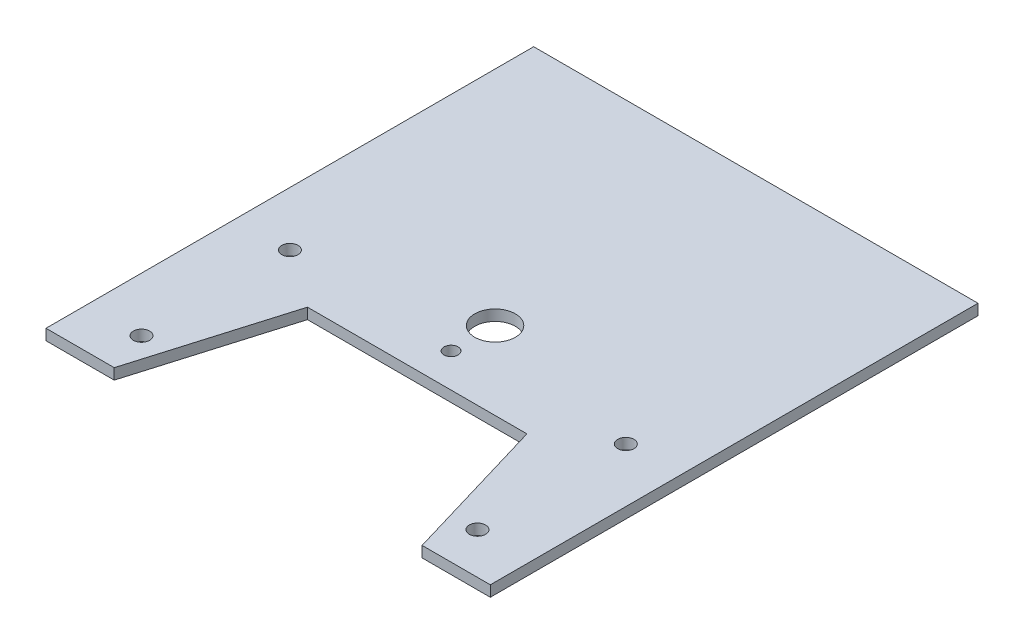
SolidWorks part; units mm, degrees
ref_plane "Front Plane" through (0, 0, 0) normal (0, 0, 1) x (1, 0, 0)
ref_plane "Top Plane" through (0, 0, 0) normal (0, 1, 0) x (1, 0, 0)
ref_plane "Right Plane" through (0, 0, 0) normal (1, 0, 0) x (0, 0, -1)
sketch "Sketch1" plane through (0, 0, 0) normal (0, 1, 0) x (1, 0, 0)
  line L0 (85, -185) -> (40.5, -35)
  line L1 (-82, 90) -> (82, 90)
  line L2 (-82, 90) -> (-82, -90)
  line L3 (-82, -90) -> (82, -90)
  line L4 (82, 90) -> (82, -90)
  line L5 (-82, 90) -> (82, -90) construction
  line L6 (-82, -90) -> (82, 90) construction
  line L7 (-40.5, -35) -> (-85, -185)
  line L8 (85, -185) -> (-85, -185)
  line L9 (40.5, -35) -> (-40.5, -35)
  line L10 (0, 90) -> (0, -90) construction
  point P0 (0, 0)
  point P8 (0, -35)
  point P13 (0, -185)
  dimension "D1" = 164
  dimension "D2" = 180
  dimension "D3" = 81
  dimension "D4" = 85
  dimension "D5" = 55
  dimension "D6" = 85
  dimension "D7" = 150
extrude "Boss-Extrude3" add sketch "Sketch1" along normal blind 4 contours L9 L0 L3 L4 L1 L2 L7
sketch "Sketch3" plane through (-73, 4, 0) normal (0, 1, 0) x (0, 0, 1)
  line L0 (-90, -9) -> (-0.5, -9)
  line L1 (-90, 73) -> (35, 73) construction
  line L2 (-90, -1) -> (-0.5, -1)
  line L12 (-90, -9) -> (-90, 155) construction
  line L18 (35, 113.5) -> (35, 32.5) construction
  line L23 (-0.5, -9) -> (-0.5, 155) construction
  line L24 (-90, -9) -> (-0.5, -9)
  line L25 (-90, -9) -> (-90, -1)
  line L26 (-90, -1) -> (-0.5, -1)
  line L27 (-0.5, -9) -> (-0.5, -1)
  line L28 (-90, 155) -> (90, 155) construction
  line L29 (-90, -5) -> (-0.5, -5) construction
  line L34 (-90, 151) -> (-0.5, 151) construction
  line L37 (-90, 147) -> (-0.5, 147)
  line L38 (-90, 147) -> (-82, 147)
  line L39 (-90, 147) -> (-90, -1)
  line L40 (-90, -1) -> (-82, -1)
  line L41 (-82, 147) -> (-82, -1)
  line L42 (-86, -1) -> (-86, 147) construction
  line L43 (-0.5, 155) -> (-0.5, 147)
  line L44 (-90, 155) -> (-0.5, 155)
  line L45 (-90, 155) -> (-90, 147)
  line L51 (35, 32.5) -> (90, 16.1833) construction
  line L52 (90, -9) -> (82, -9)
  line L53 (90, -9) -> (90, 18.5567)
  line L54 (90, 18.5567) -> (82, 18.5567)
  line L55 (82, -9) -> (82, 18.5567)
  circle A11 centre (-45.25, -5) radius 2.1
  circle A25 centre (-86, -5) radius 2.1
  circle A26 centre (-86, 34) radius 2.1
  circle A27 centre (-86, 73) radius 2.1
  circle A28 centre (-86, 112) radius 2.1
  circle A29 centre (-86, 151) radius 2.1
  circle A30 centre (-4.5, -5) radius 2.1
  circle A31 centre (-4.5, 151) radius 2.1
  circle A32 centre (-45.25, 151) radius 2.1
  circle A33 centre (86, 7.59) radius 2.1
  circle A34 centre (86, 138.41) radius 2.1
  point P38 (-82, 73)
  dimension "D1" = 8
  dimension "D2" = 89.5
  dimension "D4" = 4.2
  dimension "D3" = 8
  dimension "D5" = 40.75
  dimension "D6" = 5
  dimension "D7" = 4
  dimension "D8" = 8
  dimension "D9" = 4
  dimension "D10" = 16.59
extrude "Cut-Extrude2" [suppressed] cut sketch "Sketch3" against normal blind 10
sketch "Sketch5" plane through (0, 4, 0) normal (0, 1, 0) x (1, 0, 0)
  line L0 (82, 90) -> (82, -90) construction
  line L1 (56.8167, -90) -> (82, -90) construction
  line L2 (0, 90) -> (0, -35) construction
  line L3 (-82, 90) -> (82, 90) construction
  line L4 (40.5, -35) -> (-40.5, -35) construction
  circle A0 centre (62, -74.75) radius 3
  circle A1 centre (62, -19.99) radius 3
  circle A2 centre (-62, -74.75) radius 3
  circle A3 centre (-62, -19.99) radius 3
  circle A4 centre (0, -6.25) radius 7.5
  circle A5 centre (0, -22.5) radius 2.6
  dimension "D1" = 6
  dimension "D5" = 15
  dimension "D7" = 5.2
  dimension "D2" = 20
  dimension "D3" = 15.25
  dimension "D4" = 54.76
  dimension "D6" = 28.75
  dimension "D8" = 16.25
extrude "Cut-Extrude3" cut sketch "Sketch5" against normal up to next contours A2 | A3 | A0 | A1 | A4 | A5
sketch "Sketch6" plane through (0, 4, 0) normal (0, 1, 0) x (1, 0, 0)
  line L0 (0, 90) -> (0, -35) construction
  line L1 (-82, 90) -> (82, 90) construction
  line L2 (40.5, -35) -> (-40.5, -35) construction
  line L3 (-60, 29.25) -> (0, 29.25) construction
  line L4 (-60, 4.5) -> (-60, 54)
  line L5 (-60, 4.5) -> (60, 4.5)
  line L6 (60, 4.5) -> (60, 54)
  line L7 (-60, 54) -> (60, 54)
  line L8 (-60, 4.5) -> (60, 54) construction
  line L9 (60, 4.5) -> (-60, 54) construction
  circle A0 centre (-56, 8.5) radius 1.25
  circle A1 centre (-56, 50) radius 1.25
  circle A4 centre (56, 50) radius 1.25
  circle A5 centre (56, 8.5) radius 1.25
  point P6 (0, 29.25)
  point P23 (0, 54)
  dimension "D2" = 2.5
  dimension "D1" = 4
  dimension "D3" = 120
  dimension "D4" = 49.5
  dimension "D5" = 36
extrude "Cut-Extrude4" [suppressed] cut sketch "Sketch6" against normal up to next contours A1 | A0 | A5 | A4
